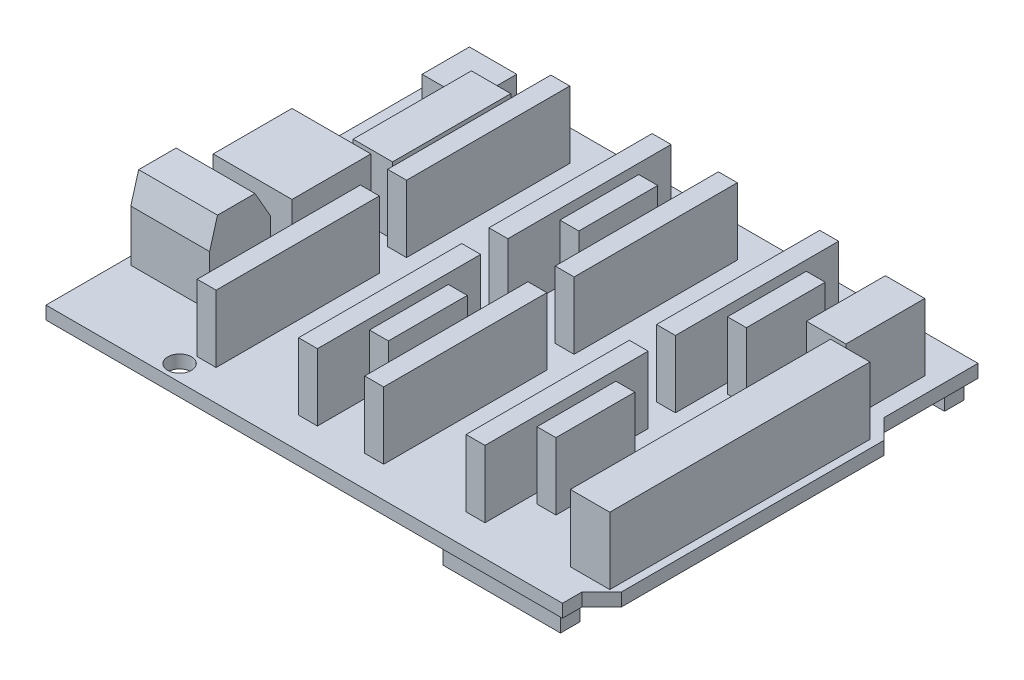
SolidWorks part; units mm, degrees
ref_plane "Front Plane" through (0, 0, 0) normal (0, 0, 1) x (1, 0, 0)
ref_plane "Top Plane" through (0, 0, 0) normal (0, 1, 0) x (1, 0, 0)
ref_plane "Right Plane" through (0, 0, 0) normal (1, 0, 0) x (0, 0, -1)
sketch "Sketch1" plane through (0, 0, 0) normal (0, 1, 0) x (1, 0, 0)
  line L0 (68, 5) -> (65.5, 2.5)
  line L1 (0, 0) -> (65.5, 0)
  line L2 (0, 0) -> (0, 52.7)
  line L4 (68, 5) -> (68, 38.25)
  line L5 (0, 0) -> (68, 52.7) construction
  line L6 (0, 52.7) -> (68, 0) construction
  line L7 (65.5, 2.5) -> (65.5, 0)
  line L12 (67.9213, 0) -> (68, 0) construction
  line L13 (68, 0) -> (68, 5) construction
  line L14 (68, 52.7) -> (68, 38.25) construction
  line L15 (0, 52.7) -> (65.5, 52.7)
  line L16 (65.5, 0) -> (67.9213, 0) construction
  line L17 (68, 38.25) -> (65.5, 40.75)
  line L18 (65.5, 40.75) -> (65.5, 52.7)
  line L19 (68, 52.7) -> (65.5, 52.7) construction
  circle A0 centre (13.75, 50.4) radius 1.5
  circle A1 centre (14.9, 2.04) radius 1.5
  point P4 (34, 26.35)
  point P17 (12.25, 50.4)
  point P18 (13.75, 51.9)
  point P19 (13.4, 2.04)
  point P20 (14.9, 0.54)
  dimension "D8" = 3
  dimension "D9" = 3
  dimension "D1" = 52.7
  dimension "D2" = 68
  dimension "D3" = 45
  dimension "D4" = 45
  dimension "D5" = 2.5
  dimension "D6" = 2.5
  dimension "D7" = 33.25
  dimension "D10" = 0.8
  dimension "D11" = 13.4
  dimension "D12" = 12.25
  dimension "D13" = 0.54
extrude "Boss-Extrude1" add sketch "Sketch1" along normal blind 1.65
sketch "Sketch2" plane through (0, 0, 0) normal (0, -1, 0) x (-1, 0, 0)
  line L0 (-65.5, 40.75) -> (-65.5, 52.7) construction
  line L1 (-64.5, 0.75) -> (-49.6, 0.75)
  line L2 (-64.5, 0.75) -> (-64.5, 3.25)
  line L3 (-64.5, 3.25) -> (-49.6, 3.25)
  line L4 (-49.6, 0.75) -> (-49.6, 3.25)
  line L5 (-64.5, 0.75) -> (-49.6, 3.25) construction
  line L6 (-64.5, 3.25) -> (-49.6, 0.75) construction
  line L7 (-64.5, 51.95) -> (-60, 51.95)
  line L8 (-64.5, 51.95) -> (-64.5, 49.45)
  line L9 (-64.5, 49.45) -> (-60, 49.45)
  line L10 (-60, 51.95) -> (-60, 49.45)
  line L11 (-64.5, 51.95) -> (-60, 49.45) construction
  line L12 (-64.5, 49.45) -> (-60, 51.95) construction
  line L13 (-32, 51.95) -> (-22.5, 51.95)
  line L14 (-32, 51.95) -> (-32, 49.45)
  line L15 (-32, 49.45) -> (-22.5, 49.45)
  line L16 (-22.5, 51.95) -> (-22.5, 49.45)
  line L17 (-32, 51.95) -> (-22.5, 49.45) construction
  line L18 (-32, 49.45) -> (-22.5, 51.95) construction
  line L19 (-65.5, 0) -> (-65.5, 2.5) construction
  line L20 (0, 0) -> (-65.5, 0) construction
  line L21 (-65.5, 52.7) -> (0, 52.7) construction
  circle A0 centre (-13.75, 50.4) radius 1.5 construction
  point P4 (-57.05, 2)
  point P9 (-62.25, 50.7)
  point P14 (-27.25, 50.7)
  dimension "D1" = 2.5
  dimension "D2" = 14.9
  dimension "D3" = 4.5
  dimension "D4" = 9.5
  dimension "D5" = 8.75
  dimension "D6" = 1
  dimension "D7" = 1
  dimension "D8" = 0.75
  dimension "D9" = 0.75
extrude "Boss-Extrude2" add sketch "Sketch2" along normal blind 2.5
sketch "Sketch3" plane through (0, 1.65, 0) normal (0, 1, 0) x (1, 0, 0)
  line L0 (0, 52.7) -> (0, 0) construction
  line L1 (9.75, 44.2) -> (14.75, 44.2)
  line L2 (9.75, 44.2) -> (9.75, 29.2)
  line L3 (9.75, 29.2) -> (14.75, 29.2)
  line L4 (14.75, 44.2) -> (14.75, 29.2)
  line L5 (9.75, 44.2) -> (14.75, 29.2) construction
  line L6 (9.75, 29.2) -> (14.75, 44.2) construction
  line L7 (2.5, 28.7) -> (12.5, 28.7)
  line L8 (2.5, 28.7) -> (2.5, 18.7)
  line L9 (2.5, 18.7) -> (12.5, 18.7)
  line L10 (12.5, 28.7) -> (12.5, 18.7)
  line L11 (2.5, 28.7) -> (12.5, 18.7) construction
  line L12 (2.5, 18.7) -> (12.5, 28.7) construction
  line L13 (15.25, 3.925) -> (17.65, 3.925)
  line L14 (15.25, 3.925) -> (15.25, 24.625)
  line L15 (15.25, 24.625) -> (17.65, 24.625)
  line L16 (17.65, 3.925) -> (17.65, 24.625)
  line L17 (15.25, 3.925) -> (17.65, 24.625) construction
  line L18 (15.25, 24.625) -> (17.65, 3.925) construction
  line L19 (28.1, 3.925) -> (30.5, 3.925)
  line L20 (28.1, 3.925) -> (28.1, 24.625)
  line L21 (28.1, 24.625) -> (30.5, 24.625)
  line L22 (30.5, 3.925) -> (30.5, 24.625)
  line L23 (28.1, 3.925) -> (30.5, 24.625) construction
  line L24 (28.1, 24.625) -> (30.5, 3.925) construction
  line L25 (36.5, 3.925) -> (38.9, 3.925)
  line L26 (36.5, 3.925) -> (36.5, 24.625)
  line L27 (36.5, 24.625) -> (38.9, 24.625)
  line L28 (38.9, 3.925) -> (38.9, 24.625)
  line L29 (36.5, 3.925) -> (38.9, 24.625) construction
  line L30 (36.5, 24.625) -> (38.9, 3.925) construction
  line L31 (49.35, 3.925) -> (51.75, 3.925)
  line L32 (49.35, 3.925) -> (49.35, 24.625)
  line L33 (49.35, 24.625) -> (51.75, 24.625)
  line L34 (51.75, 3.925) -> (51.75, 24.625)
  line L35 (49.35, 3.925) -> (51.75, 24.625) construction
  line L36 (49.35, 24.625) -> (51.75, 3.925) construction
  line L37 (15.25, 28.075) -> (17.65, 28.075)
  line L38 (15.25, 28.075) -> (15.25, 48.775)
  line L39 (15.25, 48.775) -> (17.65, 48.775)
  line L40 (17.65, 28.075) -> (17.65, 48.775)
  line L41 (15.25, 28.075) -> (17.65, 48.775) construction
  line L42 (15.25, 48.775) -> (17.65, 28.075) construction
  line L43 (28.1, 28.075) -> (30.5, 28.075)
  line L44 (28.1, 28.075) -> (28.1, 48.775)
  line L45 (28.1, 48.775) -> (30.5, 48.775)
  line L46 (30.5, 28.075) -> (30.5, 48.775)
  line L47 (28.1, 28.075) -> (30.5, 48.775) construction
  line L48 (28.1, 48.775) -> (30.5, 28.075) construction
  line L49 (36.5, 28.075) -> (38.9, 28.075)
  line L50 (36.5, 28.075) -> (36.5, 48.775)
  line L51 (36.5, 48.775) -> (38.9, 48.775)
  line L52 (38.9, 28.075) -> (38.9, 48.775)
  line L53 (36.5, 28.075) -> (38.9, 48.775) construction
  line L54 (36.5, 48.775) -> (38.9, 28.075) construction
  line L55 (49.35, 28.075) -> (51.75, 28.075)
  line L56 (49.35, 28.075) -> (49.35, 48.775)
  line L57 (49.35, 48.775) -> (51.75, 48.775)
  line L58 (51.75, 28.075) -> (51.75, 48.775)
  line L59 (49.35, 28.075) -> (51.75, 48.775) construction
  line L60 (49.35, 48.775) -> (51.75, 28.075) construction
  line L61 (58.5, 47.95) -> (63.5, 47.95)
  line L62 (58.5, 47.95) -> (58.5, 37.95)
  line L63 (58.5, 37.95) -> (63.5, 37.95)
  line L64 (63.5, 47.95) -> (63.5, 37.95)
  line L65 (58.5, 47.95) -> (63.5, 37.95) construction
  line L66 (58.5, 37.95) -> (63.5, 47.95) construction
  line L67 (67, 37.5) -> (62, 37.5)
  line L68 (67, 37.5) -> (67, 4.5)
  line L69 (67, 4.5) -> (62, 4.5)
  line L70 (62, 37.5) -> (62, 4.5)
  line L71 (67, 37.5) -> (62, 4.5) construction
  line L72 (67, 4.5) -> (62, 37.5) construction
  line L73 (34.15, 9.275) -> (31.75, 9.275)
  line L74 (34.15, 9.275) -> (34.15, 19.275)
  line L75 (34.15, 19.275) -> (31.75, 19.275)
  line L76 (31.75, 9.275) -> (31.75, 19.275)
  line L77 (34.15, 9.275) -> (31.75, 19.275) construction
  line L78 (34.15, 19.275) -> (31.75, 9.275) construction
  line L79 (34.15, 33.425) -> (31.75, 33.425)
  line L80 (34.15, 33.425) -> (34.15, 43.425)
  line L81 (34.15, 43.425) -> (31.75, 43.425)
  line L82 (31.75, 33.425) -> (31.75, 43.425)
  line L83 (34.15, 33.425) -> (31.75, 43.425) construction
  line L84 (34.15, 43.425) -> (31.75, 33.425) construction
  line L85 (55.4, 33.425) -> (53, 33.425)
  line L86 (55.4, 33.425) -> (55.4, 43.425)
  line L87 (55.4, 43.425) -> (53, 43.425)
  line L88 (53, 33.425) -> (53, 43.425)
  line L89 (55.4, 33.425) -> (53, 43.425) construction
  line L90 (55.4, 43.425) -> (53, 33.425) construction
  line L91 (55.4, 9.275) -> (53, 9.275)
  line L92 (55.4, 9.275) -> (55.4, 19.275)
  line L93 (55.4, 19.275) -> (53, 19.275)
  line L94 (53, 9.275) -> (53, 19.275)
  line L95 (55.4, 9.275) -> (53, 19.275) construction
  line L96 (55.4, 19.275) -> (53, 9.275) construction
  line L97 (65.5, 52.7) -> (0, 52.7) construction
  line L100 (0, 0) -> (65.5, 0) construction
  line L101 (68, 5) -> (68, 38.25) construction
  line L102 (65.5, 40.75) -> (65.5, 52.7) construction
  point P4 (12.25, 36.7)
  point P9 (7.5, 23.7)
  point P14 (16.45, 14.275)
  point P19 (29.3, 14.275)
  point P24 (37.7, 14.275)
  point P29 (50.55, 14.275)
  point P34 (16.45, 38.425)
  point P39 (29.3, 38.425)
  point P44 (37.7, 38.425)
  point P49 (50.55, 38.425)
  point P54 (61, 42.95)
  point P59 (64.5, 21)
  point P64 (32.95, 14.275)
  point P69 (32.95, 38.425)
  point P74 (54.2, 38.425)
  point P79 (54.2, 14.275)
  dimension "D1" = 5
  dimension "D2" = 33
  dimension "D3" = 10
  dimension "D4" = 15
  dimension "D5" = 10
  dimension "D6" = 10
  dimension "D7" = 2.4
  dimension "D8" = 10.45
  dimension "D9" = 10.45
  dimension "D10" = 1.25
  dimension "D11" = 1.25
  dimension "D12" = 3.45
  dimension "D13" = 20.7
  dimension "D14" = 6
  dimension "D15" = 15.25
  dimension "D16" = 3.925
  dimension "D17" = 10
  dimension "D18" = 2.5
  dimension "D19" = 24
  dimension "D20" = 9.75
  dimension "D21" = 8.5
  dimension "D22" = 4.5
  dimension "D23" = 1
  dimension "D24" = 4.75
  dimension "D25" = 2
extrude "Boss-Extrude3" add sketch "Sketch3" along normal blind 8.5
sketch "Sketch4" plane through (0, 1.65, 0) normal (0, 1, 0) x (1, 0, 0)
  line L0 (0, 0) -> (65.5, 0) construction
  line L1 (1, 17.5) -> (11, 17.5)
  line L2 (1, 17.5) -> (1, 9.75)
  line L3 (1, 9.75) -> (11, 9.75)
  line L4 (11, 17.5) -> (11, 9.75)
  line L5 (1, 17.5) -> (11, 9.75) construction
  line L6 (1, 9.75) -> (11, 17.5) construction
  line L7 (0, 52.7) -> (0, 0) construction
  point P4 (6, 13.625)
  dimension "D1" = 10
  dimension "D2" = 7.75
  dimension "D3" = 9.75
  dimension "D4" = 1
extrude "Boss-Extrude4" add sketch "Sketch4" along normal blind 10 contours L3 L4 L1 L2
sketch "Sketch5" plane through (1, 0, 0) normal (-1, 0, 0) x (0, 0, 1)
  line L0 (-17.5, 8.15) -> (-15.5, 11.65)
  line L1 (-17.5, 11.65) -> (-17.5, 1.65) construction
  line L2 (-17.5, 11.65) -> (-9.75, 11.65) construction
  line L3 (-15.5, 11.65) -> (-17.5, 11.65)
  line L4 (-17.5, 11.65) -> (-17.5, 8.15)
  line L5 (-9.75, 11.65) -> (-9.75, 8.15)
  line L6 (-9.75, 11.65) -> (-9.75, 1.65) construction
  line L7 (-9.75, 8.15) -> (-10.75, 11.65)
  line L8 (-9.75, 11.65) -> (-10.75, 11.65)
  dimension "D1" = 1
  dimension "D2" = 2
  dimension "D3" = 3.5
  dimension "D4" = 3.5
extrude "Cut-Extrude1" cut sketch "Sketch5" against normal blind 10 contours L0 L3 L4
sketch "Sketch6" plane through (0, 1.65, 0) normal (0, 1, 0) x (1, 0, 0)
  line L0 (65.5, 52.7) -> (0, 52.7) construction
  line L1 (2, 51.7) -> (8, 51.7)
  line L2 (2, 51.7) -> (2, 45.7)
  line L3 (2, 45.7) -> (8, 45.7)
  line L4 (8, 51.7) -> (8, 45.7)
  line L5 (2, 51.7) -> (8, 45.7) construction
  line L6 (2, 45.7) -> (8, 51.7) construction
  line L7 (0, 52.7) -> (0, 0) construction
  point P4 (5, 48.7)
  dimension "D1" = 6
  dimension "D2" = 6
  dimension "D3" = 1
  dimension "D4" = 2
extrude "Boss-Extrude5" add sketch "Sketch6" along normal blind 3.5
